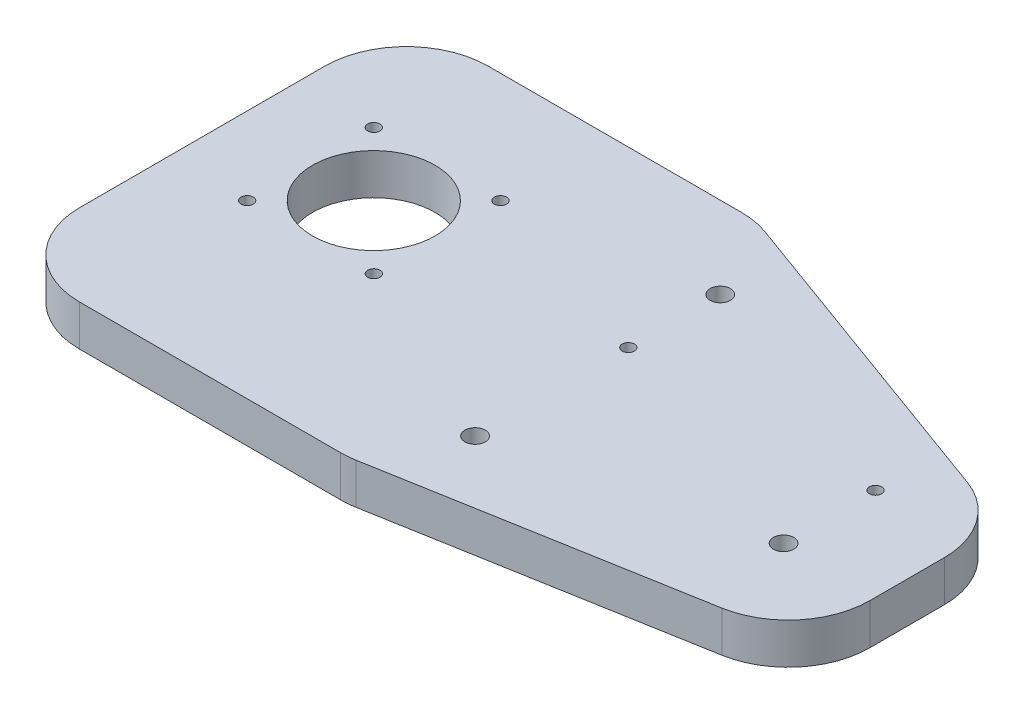
SolidWorks part; units mm, degrees
ref_plane "Front Plane" through (0, 0, 0) normal (0, 0, 1) x (1, 0, 0)
ref_plane "Top Plane" through (0, 0, 0) normal (0, 1, 0) x (1, 0, 0)
ref_plane "Right Plane" through (0, 0, 0) normal (1, 0, 0) x (0, 0, -1)
sketch "Sketch2" plane through (0, 0, 0) normal (0, 1, 0) x (1, 0, 0)
  line L0 (0, 20) -> (0, 80)
  line L1 (20, 100) -> (82.081, 100)
  line L2 (88.9214, 98.7939) -> (166.8404, 70.4336)
  line L3 (180, 51.6398) -> (180, 33.4259)
  line L4 (163.473, 13.7298) -> (87.3307, 0.3038)
  line L5 (83.8577, 0) -> (20, 0)
  line L6 (96.8, 80) -> (96.8, 35) construction
  line L7 (34.5, 75.2459) -> (34.5, 37.6789) construction
  line L8 (13.5, 36.5) -> (55.5, 36.5)
  line L9 (13.5, 36.5) -> (13.5, 78.5)
  line L10 (13.5, 78.5) -> (55.5, 78.5)
  line L11 (55.5, 36.5) -> (55.5, 78.5)
  line L12 (13.5, 36.5) -> (55.5, 78.5) construction
  line L13 (13.5, 78.5) -> (55.5, 36.5) construction
  line L14 (17.1358, 57.5) -> (53.2071, 57.5) construction
  circle A0 centre (96.8, 80) radius 2.5
  circle A1 centre (96.8, 20) radius 2.5
  circle A2 centre (157.3, 35) radius 2.5
  circle A3 centre (34.5, 57.5) radius 15
  arc A4 (82.081, 100) -> (88.9214, 98.7939) centre (82.081, 80) cw
  arc A5 (166.8404, 70.4336) -> (180, 51.6398) centre (160, 51.6398) cw
  arc A6 (180, 33.4259) -> (163.473, 13.7298) centre (160, 33.4259) cw
  arc A7 (87.3307, 0.3038) -> (83.8577, 0) centre (83.8577, 20) cw
  arc A8 (0, 20) -> (20, 0) centre (20, 20) ccw
  arc A9 (0, 80) -> (20, 100) centre (20, 80) cw
  circle A10 centre (19, 73) radius 1.5
  circle A13 centre (50, 73) radius 1.5
  circle A14 centre (19, 42) radius 1.5
  circle A15 centre (50, 42) radius 1.5
  circle A16 centre (96.8, 57.5) radius 1.5
  circle A17 centre (157.3, 57.5) radius 1.5
  point P18 (96.8, 57.5)
  point P24 (85.6075, 100)
  point P27 (180, 65.6439)
  point P30 (180, 16.6439)
  point P33 (85.6075, 0)
  point P36 (0, 0)
  point P39 (0, 100)
  dimension "D8" = 30
  dimension "D12" = 41.3
  dimension "D14" = 5
  dimension "D15" = 5
  dimension "D16" = 5
  dimension "D19" = 20
  dimension "D21" = 3
  dimension "D22" = 3
  dimension "D23" = 3
  dimension "D1" = 100
  dimension "D2" = 60
  dimension "D3" = 20
  dimension "D4" = 45
  dimension "D5" = 60.5
  dimension "D6" = 10
  dimension "D7" = 20
  dimension "D9" = 45
  dimension "D10" = 42
  dimension "D11" = 42
  dimension "D13" = 13.5
  dimension "D17" = 49
  dimension "D18" = 180
  dimension "D20" = 15.5
extrude "Boss-Extrude1" add sketch "Sketch2" along normal blind 10 contours A9 L0 A8 L5 A7 L4 A6 L3 A5 L2 A4 L1 A2 A1 A0 L11 L8 L9 L10 | L8 L11 L10 L9 A15 A13 A10 A3 A14
